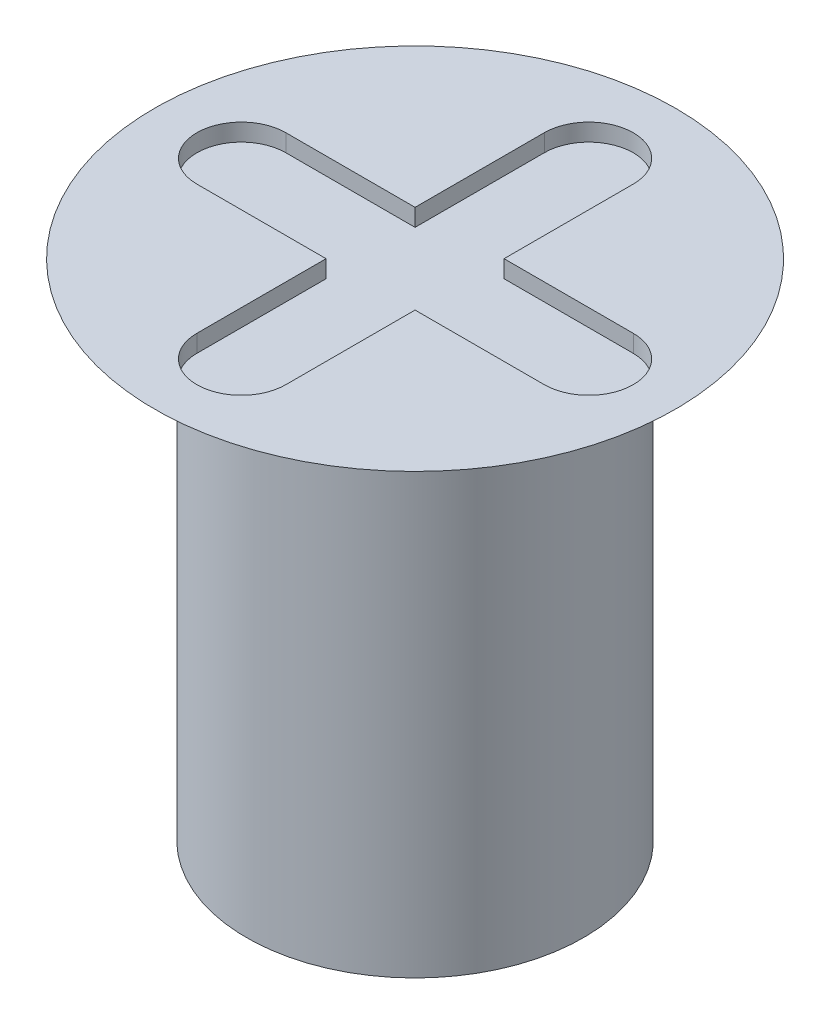
SolidWorks part; units mm, degrees
ref_plane "Front Plane" through (0, 0, 0) normal (0, 0, 1) x (1, 0, 0)
ref_plane "Top Plane" through (0, 0, 0) normal (0, 1, 0) x (1, 0, 0)
ref_plane "Right Plane" through (0, 0, 0) normal (1, 0, 0) x (0, 0, -1)
sketch "Sketch1" plane through (0, 0, 0) normal (0, 0, 1) x (1, 0, 0)
  line L0 (0, 0) -> (0, 12.9627) construction
  line L1 (0, 2.9) -> (1.5, 2.9)
  line L2 (1.5, 2.9) -> (0.97, 2.594)
  line L3 (0.97, 2.594) -> (0.97, 0)
  line L4 (0.97, 0) -> (0, 0)
  line L5 (0, 0) -> (0, 2.9)
  dimension "D1" = 2.9
  dimension "D2" = 1.94
  dimension "D3" = 60
  dimension "D4" = 3
revolve "Revolve1" add sketch "Sketch1" angle 360 about L0
sketch "Sketch2" plane through (0, 2.9, 0) normal (0, 1, 0) x (1, 0, 0)
  line L0 (0, 1) -> (0, -1) construction
  line L1 (0.2561, 1) -> (0.2561, 0.2561)
  line L2 (-0.2561, 1) -> (-0.2561, 0.2561)
  line L3 (-1, 0) -> (1, 0) construction
  line L4 (-1, 0.2561) -> (-0.2561, 0.2561)
  line L5 (-1, -0.2561) -> (-0.2561, -0.2561)
  line L6 (0.2561, 0.2561) -> (1, 0.2561)
  line L7 (-0.2561, -0.2561) -> (-0.2561, -1)
  line L8 (0.2561, -0.2561) -> (1, -0.2561)
  line L9 (0.2561, -0.2561) -> (0.2561, -1)
  arc A0 (0.2561, 1) -> (-0.2561, 1) centre (0, 1) ccw
  arc A1 (-0.2561, -1) -> (0.2561, -1) centre (0, -1) ccw
  arc A2 (-1, 0.2561) -> (-1, -0.2561) centre (-1, 0) ccw
  arc A3 (1, -0.2561) -> (1, 0.2561) centre (1, 0) ccw
  point P2 (0, 0)
  point P9 (0, 0)
  point P14 (0, 0)
  point P19 (0, 0)
  dimension "D2" = 0.2561
  dimension "D1" = 2
extrude "Cut-Extrude1" cut sketch "Sketch2" against normal blind 0.1
